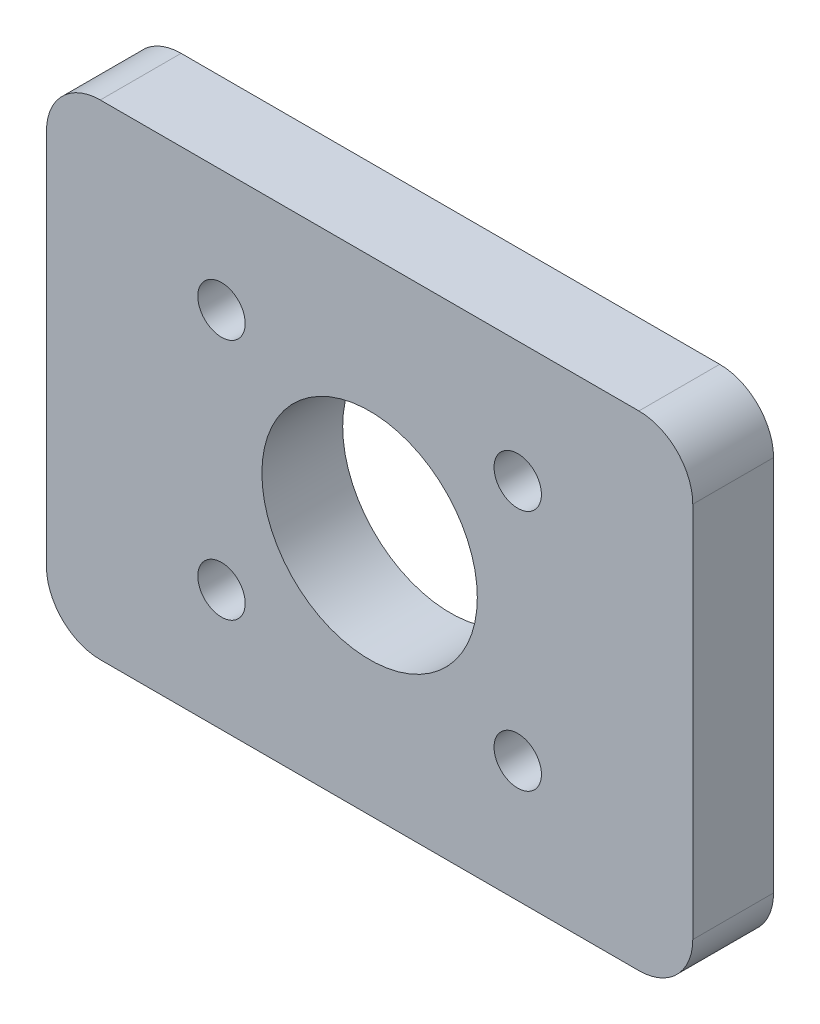
SolidWorks part; units mm, degrees
ref_plane "Front Plane" through (0, 0, 0) normal (0, 0, 1) x (1, 0, 0)
ref_plane "Top Plane" through (0, 0, 0) normal (0, 1, 0) x (1, 0, 0)
ref_plane "Right Plane" through (0, 0, 0) normal (1, 0, 0) x (0, 0, -1)
sketch "Sketch1" plane through (0, 0, 0) normal (0, 0, 1) x (1, 0, 0)
  line L0 (-27.5, 45) -> (-27.5, -45) construction
  line L1 (-50, 45) -> (50, 45)
  line L2 (-60, 35) -> (-60, -35)
  line L3 (-50, -45) -> (50, -45)
  line L4 (60, 35) -> (60, -35)
  line L5 (-60, 45) -> (60, -45) construction
  line L6 (-60, -45) -> (60, 45) construction
  line L7 (27.5, 45) -> (27.5, -45) construction
  line L8 (-60, 22.5) -> (60, 22.5) construction
  line L9 (-60, -22.5) -> (60, -22.5) construction
  arc A0 (-60, -35) -> (-50, -45) centre (-50, -35) ccw
  arc A1 (50, -45) -> (60, -35) centre (50, -35) ccw
  arc A2 (60, 35) -> (50, 45) centre (50, 35) ccw
  arc A3 (-50, 45) -> (-60, 35) centre (-50, 35) ccw
  circle A4 centre (-27.5, 22.5) radius 4.4
  circle A5 centre (27.5, 22.5) radius 4.4
  circle A6 centre (-27.5, -22.5) radius 4.4
  circle A7 centre (27.5, -22.5) radius 4.4
  circle A8 centre (0, 0) radius 20
  point P0 (0, 0)
  dimension "D3" = 10
  dimension "D1" = 120
  dimension "D2" = 90
  dimension "D4" = 22.5
  dimension "D5" = 22.5
  dimension "D6" = 32.5
  dimension "D7" = 32.5
extrude "Boss-Extrude1" add sketch "Sketch1" along normal blind 15
